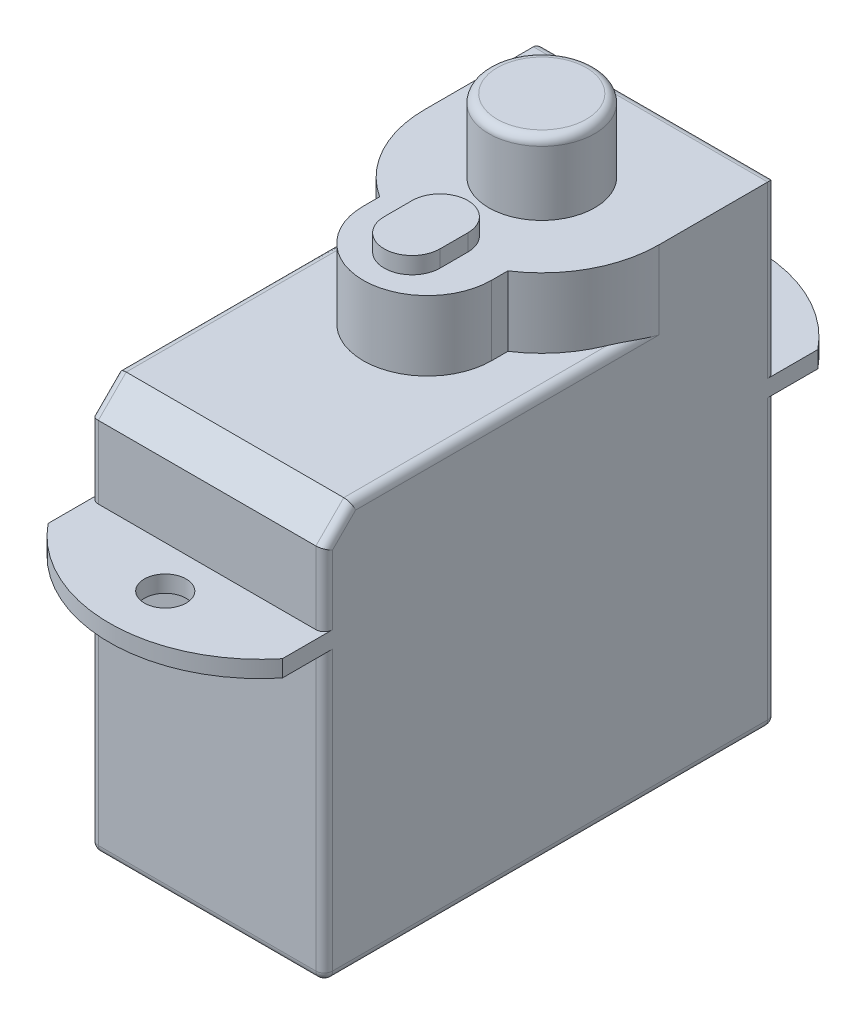
SolidWorks part; units mm, degrees
ref_plane "前视基准面" through (0, 0, 0) normal (0, 0, 1) x (1, 0, 0)
ref_plane "上视基准面" through (0, 0, 0) normal (0, 1, 0) x (1, 0, 0)
ref_plane "右视基准面" through (0, 0, 0) normal (1, 0, 0) x (0, 0, -1)
sketch "草图1" plane through (0, 0, 0) normal (0, 1, 0) x (1, 0, 0)
  line L0 (0, 0) -> (0, 16.2)
  line L1 (0, 16.2) -> (8.4, 16.2)
  line L2 (8.4, 16.2) -> (8.4, 0)
  line L3 (8.4, 0) -> (0, 0)
extrude "凸台-拉伸1" add sketch "草图1" along normal blind 14.5
ref_plane "基准面4" through (0, 10.3, 0) normal (0, -1, 0) x (-1, 0, 0)
sketch "草图3" plane through (0, 10.3, 0) normal (0, -1, 0) x (-1, 0, 0)
  line L0 (0, 16.2) -> (0, 17.7)
  line L2 (-8.4, 17.7) -> (-8.4, 16.2)
  line L3 (-8.4, 16.2) -> (0, 16.2)
  line L8 (-8.4, 0) -> (0, 0)
  line L9 (-8.4, -1.5) -> (-8.4, 0)
  line L10 (0, 0) -> (0, -1.5)
  arc A0 (-8.4, 17.7) -> (0, 17.7) centre (-4.2, 14.29) cw
  circle A1 centre (-4.2, 17.7) radius 0.75
  circle A2 centre (-4.2, -1.5) radius 0.75
  arc A3 (-8.4, -1.5) -> (0, -1.5) centre (-4.2, 1.91) ccw
extrude "凸台-拉伸2" add sketch "草图3" against normal blind 0.6
sketch "草图4" plane through (0, 14.5, 0) normal (0, 1, 0) x (1, 0, 0)
  line L2 (8.4, 12) -> (8.4, 16.2)
  line L3 (0, 16.2) -> (0, 12)
  line L4 (8.4, 16.2) -> (0, 16.2)
  line L7 (6.5, 7.9) -> (6.5, 8.4857)
  line L8 (1.9, 7.9) -> (1.9, 8.4857)
  arc A0 (0, 12) -> (1.9, 8.4857) centre (4.2, 12) ccw
  arc A1 (1.9, 7.9) -> (6.5, 7.9) centre (4.2, 7.9) ccw
  arc A2 (6.5, 8.4857) -> (8.4, 12) centre (4.2, 12) ccw
extrude "凸台-拉伸3" add sketch "草图4" along normal blind 2.5
sketch "草图5" plane through (0, 17, 0) normal (0, 1, 0) x (1, 0, 0)
  circle A0 centre (4.2, 12) radius 1.9
extrude "凸台-拉伸4" add sketch "草图5" along normal blind 2.6
sketch "草图6" plane through (0, 17, 0) normal (0, 1, 0) x (1, 0, 0)
  line L0 (5.2, 8.35) -> (5.2, 7.35)
  line L1 (3.2, 8.35) -> (3.2, 7.35)
  arc A0 (5.2, 8.35) -> (3.2, 8.35) centre (4.2, 8.35) ccw
  arc A2 (3.2, 7.35) -> (5.2, 7.35) centre (4.2, 7.35) ccw
extrude "凸台-拉伸5" add sketch "草图6" along normal blind 0.6
sketch "草图7" plane through (0, 0, -16.2) normal (0, 0, -1) x (-1, 0, 0)
  line L1 (-8.4, 0) -> (0, 0) construction
  line L2 (-4.2, 4.3) -> (-6.1, 4.3)
  line L3 (-6.1, 4.3) -> (-6.1, 0)
  line L4 (-6.1, 0) -> (-2.3, 0)
  line L5 (-4.2, 4.3) -> (-2.3, 4.3)
  line L6 (-2.3, 4.3) -> (-2.3, 0)
extrude "凸台-拉伸6" add sketch "草图7" along normal blind 0.5
chamfer "倒角1" distance 1 angle 45 1 edges at (4.2, 14.5, 0)
fillet "圆角1" radius 0.3 17 edges at (4.2, 19.6, -10.1) (1.15, 0, -16.2) (7.25, 0, -16.2) (8.4, 0, -8.1) (0, 0, -8.1) (4.2, 0, 0) (8.4, 5.15, 0) (8.4, 12.2, 0) (0, 12.2, 0) (0, 5.15, 0) (8.4, 14.5, -6.5) (0, 14.5, -6.5) (8.4, 5.15, -16.2) (0, 5.15, -16.2) (4.2, 17, -16.2) (0, 14, -0.5) (8.4, 14, -0.5)
